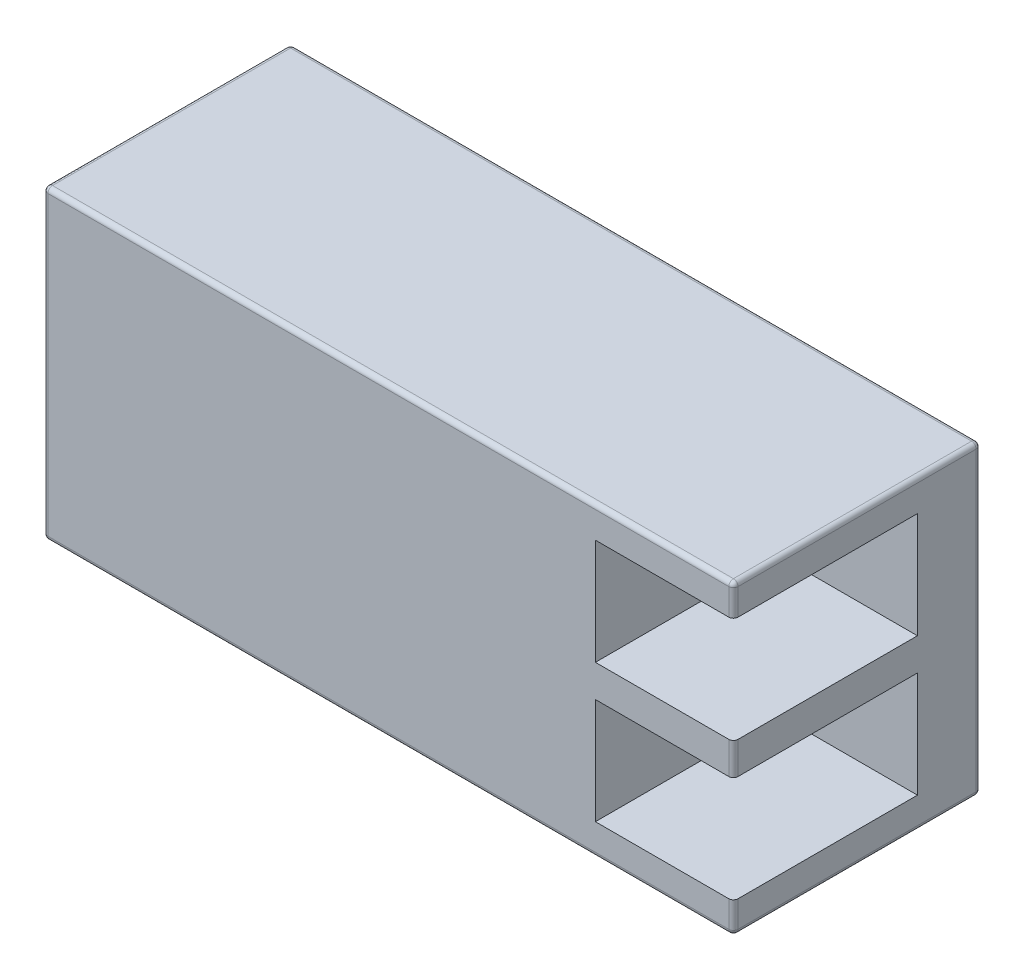
SolidWorks part; units mm, degrees
ref_plane "Front Plane" through (0, 0, 0) normal (0, 0, 1) x (1, 0, 0)
ref_plane "Top Plane" through (0, 0, 0) normal (0, 1, 0) x (1, 0, 0)
ref_plane "Right Plane" through (0, 0, 0) normal (1, 0, 0) x (0, 0, -1)
sketch "Sketch1" plane through (0, 0, 0) normal (0, 0, 1) x (1, 0, 0)
  line L1 (15, 6.65) -> (-15, 6.65)
  line L2 (15, 6.65) -> (15, -6.65)
  line L3 (15, -6.65) -> (-15, -6.65)
  line L4 (-15, 6.65) -> (-15, -6.65)
  line L5 (15, 6.65) -> (-15, -6.65) construction
  line L6 (15, -6.65) -> (-15, 6.65) construction
  point P0 (0, 0)
  dimension "D1" = 13.3
  dimension "D2" = 30
extrude "Boss-Extrude1" add sketch "Sketch1" along normal blind 10.75
sketch "Sketch2" plane through (15, 0, 0) normal (1, 0, 0) x (0, 0, -1)
  line L0 (-10.75, -6.65) -> (-10.75, 6.65) construction
  line L5 (-10.75, -0.7) -> (-2.75, -0.7)
  line L6 (-10.75, -0.7) -> (-10.75, -5.3)
  line L7 (-10.75, -5.3) -> (-2.75, -5.3)
  line L8 (-2.75, -0.7) -> (-2.75, -5.3)
  line L9 (-10.75, 0) -> (0, 0) construction
  line L10 (0, -6.65) -> (0, 6.65) construction
  line L11 (-2.75, 0.7) -> (-2.75, 5.3)
  line L12 (-10.75, 5.3) -> (-2.75, 5.3)
  line L13 (-10.75, 0.7) -> (-10.75, 5.3)
  line L14 (-10.75, 0.7) -> (-2.75, 0.7)
  dimension "D1" = 4.6
  dimension "D2" = 8
  dimension "D3" = 0.7
extrude "Cut-Extrude1" cut sketch "Sketch2" against normal blind 6
fillet "Fillet1" radius 0.2 14 edges at (15, 0, 10.75) (15, 5.975, 10.75) (15, -5.975, 10.75) (-15, -6.65, 5.375) (-15, 0, 0) (-15, 6.65, 5.375) (15, 6.65, 5.375) (0, 6.65, 0) (0, -6.65, 0) (15, 0, 0) (15, -6.65, 5.375) (0, 6.65, 10.75) (-15, 0, 10.75) (0, -6.65, 10.75)
